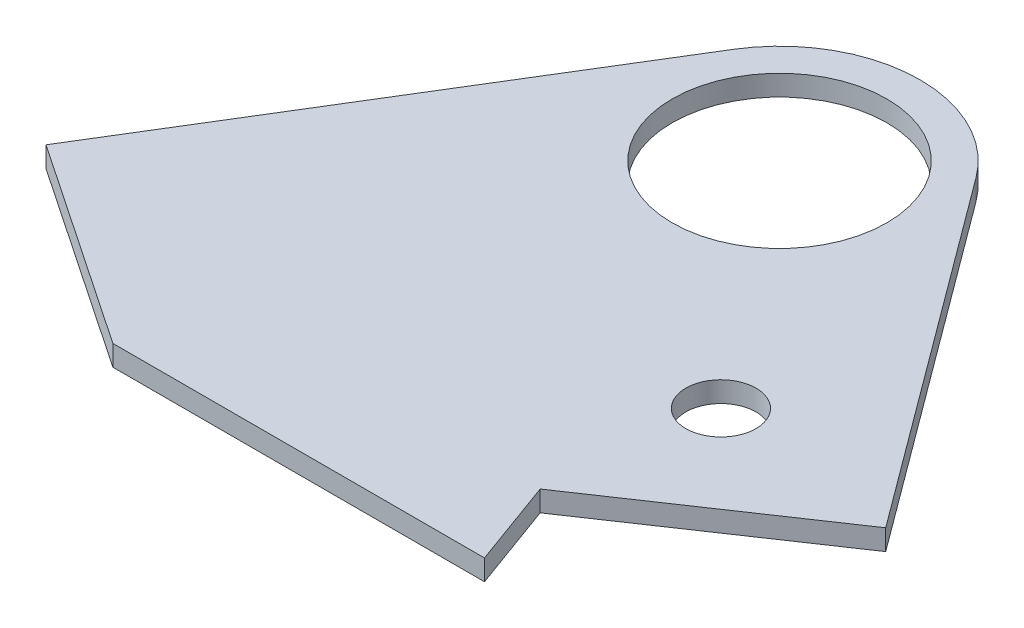
SolidWorks part; units mm, degrees
material "AISI 1020 Steel, Cold Rolled"
ref_plane "Front Plane" through (0, 0, 0) normal (0, 0, 1) x (1, 0, 0)
ref_plane "p" through (0, 0, 0) normal (0, 1, 0) x (1, 0, 0)
ref_plane "Right Plane" through (0, 0, 0) normal (1, 0, 0) x (0, 0, -1)
sketch "Sketch1" plane through (0, 0, 0) normal (0, 1, 0) x (1, 0, 0)
  line L0 (-21.2238, -59.5) -> (23.7762, -59.5)
  line L2 (-21.2238, -59.5) -> (-46.0949, -42.7242)
  line L3 (23.7762, -59.5) -> (19.9181, -48.9)
  line L4 (19.9181, -48.9) -> (44.9051, -32.0461)
  line L5 (-46.0949, -42.7242) -> (-14.4992, 8.8919)
  line L6 (13.6606, 10.1352) -> (44.9051, -32.0461)
  circle A0 centre (0, 0) radius 13
  arc A1 (-14.4992, 8.8919) -> (13.6606, 10.1352) centre (0, 0.0165) cw
  circle A2 centre (22.4051, -29.5) radius 4.25
  point P10 (-0.7498, 17)
  dimension "D1" = 26
  dimension "D11" = 17
  dimension "D12" = 8.5
  dimension "D2" = 45
  dimension "D3" = 146
  dimension "D4" = 30
  dimension "D5" = 70
  dimension "D6" = 10.6
  dimension "D7" = 34
  dimension "D8" = 91
  dimension "D9" = 68
  dimension "D10" = 0
  dimension "D13" = 30
  dimension "D14" = 22.5
  dimension "D15" = 76.5
  dimension "D16" = 59.5
extrude "Boss-Extrude1" add sketch "Sketch1" along normal mid plane 2.5
